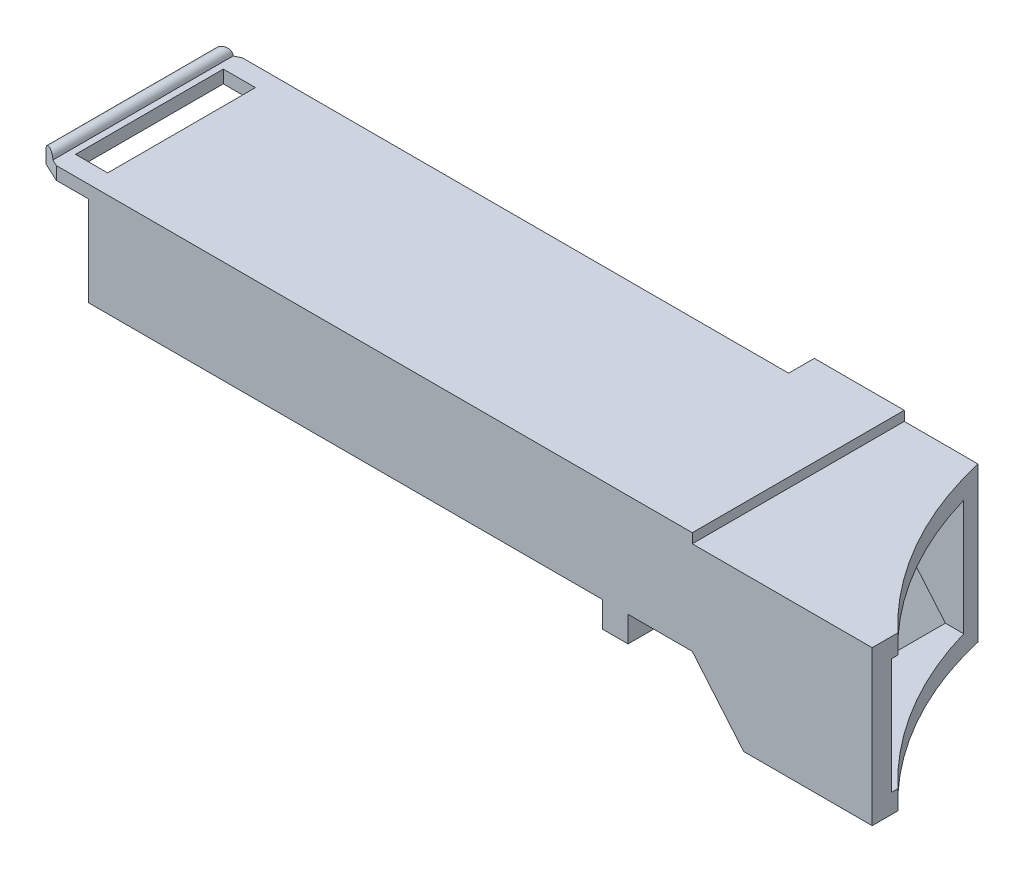
SolidWorks part; units mm, degrees
ref_plane "Plano frontal" through (0, 0, 0) normal (0, 0, 1) x (1, 0, 0)
ref_plane "Plano superior" through (0, 0, 0) normal (0, 1, 0) x (1, 0, 0)
ref_plane "Plano direito" through (0, 0, 0) normal (1, 0, 0) x (0, 0, -1)
sketch "Esboço1" plane through (0, 0, 0) normal (0, 0, 1) x (1, 0, 0)
  line L0 (9.5309, 0) -> (70, 0)
  line L1 (84, -0.75) -> (84, -12.75)
  line L2 (84, -12.75) -> (74, -12.75)
  line L3 (74, -12.75) -> (70, -8)
  line L4 (70, -8) -> (6.0021, -8)
  line L5 (70, 0) -> (70, -0.75)
  line L6 (0.134, -6.5798) -> (0, -6.9479)
  line L7 (0, -6.9479) -> (5.6382, -9)
  line L8 (5.6382, -9) -> (6.0021, -8)
  line L9 (70, -0.75) -> (84, -0.75)
  arc A0 (9.5309, 0) -> (0.134, -6.5798) centre (9.5309, -10) ccw
  point P15 (0, 0)
  dimension "D10" = 10
  dimension "D1" = 12
  dimension "D2" = 10
  dimension "D3" = 8
  dimension "D4" = 4
  dimension "D5" = 74
  dimension "D6" = 110
  dimension "D7" = 6
  dimension "D8" = 9
  dimension "D9" = 0.75
extrude "Ressalto-extrusão1" add sketch "Esboço1" along normal blind 16.5
sketch "Esboço5" plane through (0, -12.75, 0) normal (0, -1, 0) x (1, 0, 0)
  line L0 (0, 16.5) -> (0, 13.5) construction
  line L1 (0, 16.5) -> (0, 0) construction
  line L2 (0, 13.5) -> (67, 13.5) construction
  line L3 (67, 13.5) -> (70, 16.5) construction
  line L4 (6.0021, 16.5) -> (70, 16.5) construction
  line L5 (70, 16.5) -> (0, 16.5) construction
  line L7 (84, 16.5) -> (84, 0) construction
  line L8 (74, 16.5) -> (84, 16.5) construction
  line L9 (0, 0) -> (65, 0)
  line L10 (6.0021, 0) -> (70, 0) construction
  line L11 (65, 0) -> (63, 2)
  line L12 (63, 2) -> (0, 2)
  line L13 (0, 2) -> (0, 0)
  dimension "D1" = 17
  dimension "D2" = 45
  dimension "D3" = 3
  dimension "D4" = 45
  dimension "D5" = 2
  dimension "D6" = 21
extrude "Corte-extrusão3" cut sketch "Esboço5" against normal through all both and the other way through all
shell "Casca1" thickness 1.5
sketch "Esboço4" plane through (0, -12.75, 0) normal (0, -1, 0) x (1, 0, 0)
  line L0 (84, 16.5) -> (84, 0) construction
  line L1 (74, 0) -> (84, 0) construction
  line L2 (74, 16.5) -> (84, 16.5) construction
  line L3 (75.7378, 0) -> (84, 0)
  line L4 (84, 0) -> (84, 14.5)
  arc A0 (84, 14.5) -> (75.7378, 0) centre (104, -6.5) ccw
  point P14 (79, 0)
  dimension "D3" = 29
  dimension "D1" = 25
  dimension "D2" = 23
extrude "Corte-extrusão2" cut sketch "Esboço4" against normal through all
sketch "Esboço6" plane through (0, 0, 2) normal (0, 0, -1) x (-1, 0, 0)
  line L0 (-63, 0) -> (-63, -8) construction
  line L1 (37.9363, -21.7722) -> (-23, -21.7722)
  line L2 (37.9363, -21.7722) -> (37.9363, 9.9427)
  line L3 (37.9363, 9.9427) -> (-23, 9.9427)
  line L4 (-23, -21.7722) -> (-23, 9.9427)
  point P6 (27.9363, -21.7722)
  dimension "D1" = 40
extrude "Corte-extrusão4" cut sketch "Esboço6" against normal through all both and the other way through all
sketch "Esboço7" plane through (0, 0, 16.5) normal (0, 0, 1) x (1, 0, 0)
  line L0 (23, 0) -> (20, 0)
  line L1 (19, 0) -> (19, -1)
  line L2 (19, -1) -> (23, -1)
  line L3 (23, 0) -> (23, -8) construction
  line L4 (23, -1) -> (23, 0)
  arc A0 (20, 0) -> (19, 0) centre (19.5, 0) ccw
  point P10 (0, 0)
  dimension "D2" = 0.5
  dimension "D1" = 1
  dimension "D3" = 3
extrude "Ressalto-extrusão2" add sketch "Esboço7" against normal up to surface (14.5 mm away) up to face at (43, -4, 2)
sketch "Esboço8" plane through (0, -1, 0) normal (0, -1, 0) x (1, 0, 0)
  line L0 (23, 2) -> (23, 16.5) construction
  line L1 (23, 3.5) -> (20.5, 3.5)
  line L2 (23, 3.5) -> (23, 15)
  line L3 (23, 15) -> (20.5, 15)
  line L4 (20.5, 3.5) -> (20.5, 15)
  line L5 (19, 2) -> (19, 16.5) construction
  line L6 (19, 16.5) -> (23, 16.5) construction
  line L7 (19, 9.25) -> (13.318, 9.25) construction
  line L8 (20.5, 16.5) -> (19, 16.5)
  line L9 (19, 16.5) -> (19, 15.8)
  line L10 (19, 15.8) -> (20.5, 16.5)
  line L11 (19, 2.7) -> (20.5, 2)
  line L12 (19, 2) -> (19, 2.7)
  line L13 (20.5, 2) -> (19, 2)
  point P8 (19, 9.25)
  point P9 (20.5, 9.25)
  dimension "D1" = 1.5
  dimension "D2" = 1.5
  dimension "D3" = 0.7
  dimension "D4" = 1.5
extrude "Corte-extrusão5" cut sketch "Esboço8" against normal blind 10
sketch "Esboço9" plane through (0, -8, 0) normal (0, -1, 0) x (1, 0, 0)
  line L0 (23, 16.5) -> (70, 16.5) construction
  line L1 (63, 16.5) -> (65, 16.5)
  line L2 (63, 16.5) -> (63, 14.5)
  line L3 (63, 14.5) -> (65, 14.5)
  line L4 (65, 16.5) -> (65, 14.5)
  dimension "D1" = 2
  dimension "D2" = 2
extrude "Ressalto-extrusão3" add sketch "Esboço9" along normal blind 2
sketch "Esboço10" plane through (0, -8, 0) normal (0, -1, 0) x (1, 0, 0)
  line L1 (63, 2) -> (65, 2)
  line L2 (63, 2) -> (63, 0)
  line L3 (63, 0) -> (65, 0)
  line L4 (65, 2) -> (65, 0)
extrude "Ressalto-extrusão4" add sketch "Esboço10" against normal up to surface (8 mm away) up to face at (21.75, 0, 9.25)
